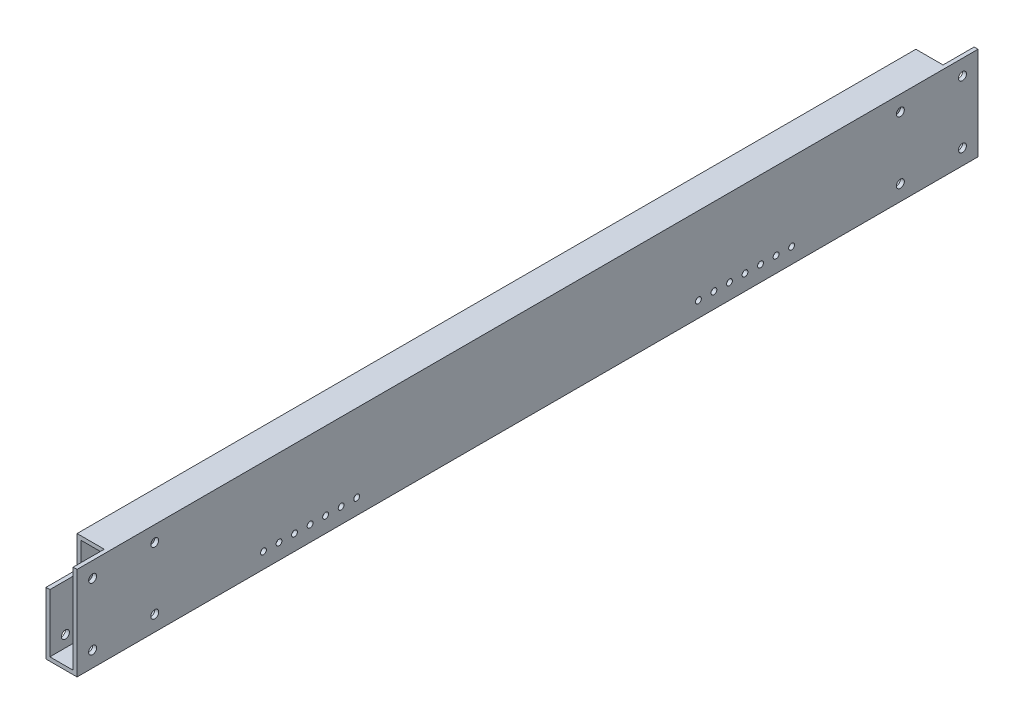
SolidWorks part; units mm, degrees
ref_plane "Front Plane" through (0, 0, 0) normal (0, 0, 1) x (1, 0, 0)
ref_plane "Top Plane" through (0, 0, 0) normal (0, 1, 0) x (1, 0, 0)
ref_plane "Right Plane" through (0, 0, 0) normal (1, 0, 0) x (0, 0, -1)
sketch "Sketch1" plane through (0, 0, 0) normal (0, 0, 1) x (1, 0, 0)
  line L1 (-12.7, -38.1) -> (12.7, -38.1)
  line L2 (-12.7, -38.1) -> (-12.7, 38.1)
  line L3 (-12.7, 38.1) -> (12.7, 38.1)
  line L4 (12.7, -38.1) -> (12.7, 38.1)
  line L5 (-12.7, -38.1) -> (12.7, 38.1) construction
  line L6 (-12.7, 38.1) -> (12.7, -38.1) construction
  point P0 (0, 0)
  dimension "D1" = 25.4
  dimension "D2" = 76.2
extrude "Boss-Extrude1" add sketch "Sketch1" along normal mid plane 736.6
shell "Shell1" thickness 3.175
sketch "Sketch3" plane through (12.7, 0, 0) normal (1, 0, 0) x (0, 0, -1)
  line L0 (368.3, -38.1) -> (368.3, 38.1) construction
  line L1 (-368.3, -38.1) -> (368.3, -38.1) construction
  line L2 (0, -53.276) -> (0, 47.534) construction
  circle A0 centre (215.9, -25.4) radius 2.3813
  circle A1 centre (203.2, -25.4) radius 2.3813
  circle A2 centre (190.5, -25.4) radius 2.3813
  circle A3 centre (177.8, -25.4) radius 2.3813
  circle A4 centre (165.1, -25.4) radius 2.3813
  circle A5 centre (152.4, -25.4) radius 2.3813
  circle A6 centre (139.7, -25.4) radius 2.3813
  circle A7 centre (-139.7, -25.4) radius 2.3813
  circle A8 centre (-152.4, -25.4) radius 2.3813
  circle A9 centre (-165.1, -25.4) radius 2.3813
  circle A10 centre (-203.2, -25.4) radius 2.3813
  circle A11 centre (-177.8, -25.4) radius 2.3813
  circle A12 centre (-215.9, -25.4) radius 2.3813
  circle A13 centre (-190.5, -25.4) radius 2.3813
  dimension "D1" = 4.7625
  dimension "D3" = 12.7
  dimension "D4" = 12.7
  dimension "D5" = 12.7
  dimension "D6" = 12.7
  dimension "D7" = 12.7
  dimension "D8" = 12.7
  dimension "D9" = 12.7
  dimension "D10" = 12.7
  dimension "D2" = 152.4
extrude "Cut-Extrude2" cut sketch "Sketch3" against normal up to next
sketch "Sketch4" plane through (-12.7, 0, 0) normal (-1, 0, 0) x (0, 0, 1)
  line L1 (-368.3, 38.1) -> (-342.9, 38.1)
  line L2 (-368.3, 38.1) -> (-368.3, 12.7)
  line L3 (-368.3, 12.7) -> (-342.9, 12.7)
  line L4 (-342.9, 38.1) -> (-342.9, 12.7)
  line L5 (368.3, 38.1) -> (342.9, 38.1)
  line L6 (368.3, 38.1) -> (368.3, 12.7)
  line L7 (368.3, 12.7) -> (342.9, 12.7)
  line L8 (342.9, 38.1) -> (342.9, 12.7)
  dimension "D1" = 25.4
  dimension "D2" = 25.4
  dimension "D3" = 25.4
  dimension "D4" = 25.4
extrude "Cut-Extrude3" cut sketch "Sketch4" against normal blind 22.225
sketch "Sketch5" plane through (9.525, 0, 0) normal (-1, 0, 0) x (0, 0, 1)
  line L0 (-342.9, 38.1) -> (-368.3, 38.1) construction
  line L1 (-368.3, -34.925) -> (-368.3, 38.1) construction
  line L2 (368.3, 38.1) -> (342.9, 38.1) construction
  line L3 (368.3, -38.1) -> (-368.3, -38.1) construction
  line L4 (368.3, -34.925) -> (368.3, 38.1) construction
  line L5 (-368.3, -38.1) -> (-368.3, 38.1) construction
  line L6 (368.3, 38.1) -> (-368.3, 38.1) construction
  line L7 (0, -56.7562) -> (0, 59.4169) construction
  circle A0 centre (-355.6, 25.4) radius 3.25
  circle A1 centre (355.6, 25.4) radius 3.25
  circle A2 centre (-355.6, -25.4) radius 3.25
  circle A3 centre (-304.8, -25.4) radius 3.25
  circle A4 centre (-304.8, 25.4) radius 3.25
  circle A5 centre (304.8, 25.4) radius 3.25
  circle A6 centre (304.8, -25.4) radius 3.25
  circle A7 centre (355.6, -25.4) radius 3.25
  dimension "D3" = 6.5
  dimension "D4" = 6.5
  dimension "D6" = 12.7
  dimension "D7" = 12.7
  dimension "D8" = 6.5
  dimension "D9" = 12.7
  dimension "D10" = 6.5
  dimension "D11" = 6.5
  dimension "D12" = 63.5
  dimension "D13" = 63.5
  dimension "D14" = 12.7
  dimension "D15" = 12.7
  dimension "D1" = 12.7
  dimension "D2" = 12.7
  dimension "D5" = 12.7
extrude "Cut-Extrude4" cut sketch "Sketch5" against normal through all and the other way through all
equation "\"robotwidth\"= 29in"
equation "\"D1@Boss-Extrude1\"=\"robotwidth\""
